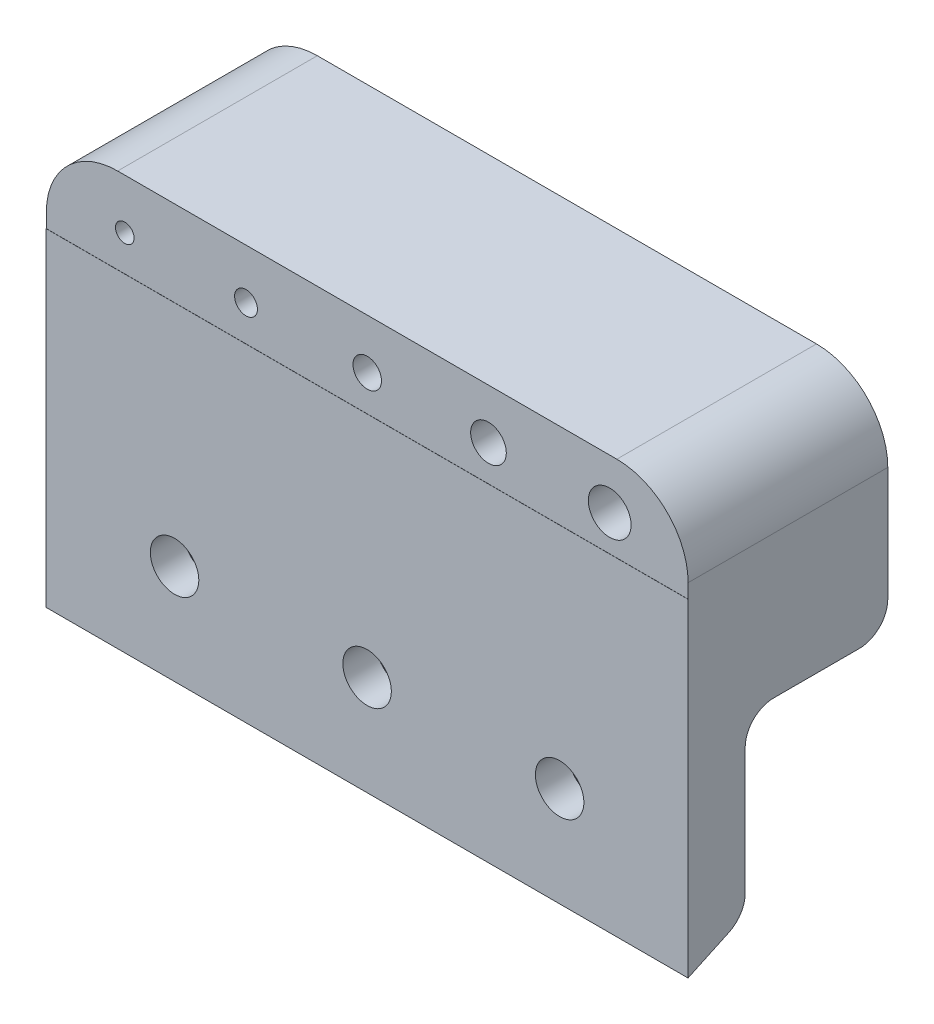
SolidWorks part; units mm, degrees
material "Alliage 2018"
ref_plane "Plan de face" through (0, 0, 0) normal (0, 0, 1) x (1, 0, 0)
ref_plane "Plan de dessus" through (0, 0, 0) normal (0, 1, 0) x (1, 0, 0)
ref_plane "Plan de droite" through (0, 0, 0) normal (1, 0, 0) x (0, 0, -1)
sketch "Esquisse1" plane through (0, 0, 0) normal (0, 0, 1) x (1, 0, 0)
  line L1 (-22.5, -14.5) -> (22.5, -14.5)
  line L2 (-22.5, -14.5) -> (-22.5, 14.5)
  line L3 (-22.5, 14.5) -> (22.5, 14.5)
  line L4 (22.5, -14.5) -> (22.5, 14.5)
  line L5 (-22.5, -14.5) -> (22.5, 14.5) construction
  line L6 (-22.5, 14.5) -> (22.5, -14.5) construction
  point P0 (0, 0)
  dimension "D1" = 29
  dimension "D2" = 45
extrude "Boss.-Extru.1" add sketch "Esquisse1" along normal blind 14 from offset 0
sketch "Esquisse8" plane through (0, 0, 14) normal (0, 0, 1) x (1, 0, 0)
  line L0 (-22.5, 14.5) -> (-22.5, -14.5) construction
  line L1 (22.5, -14.5) -> (-22.5, -14.5)
  line L2 (22.5, -14.5) -> (22.5, 8.5)
  line L3 (22.5, 8.5) -> (-22.5, 8.5)
  line L4 (-22.5, -14.5) -> (-22.5, 8.5)
  dimension "D1" = 23
extrude "Boss.-Extru.2" add sketch "Esquisse8" along normal blind 0.01
sketch "Esquisse3" plane through (0, 0, 14) normal (0, 0, 1) x (1, 0, 0)
  line L0 (-22.5, 8.5) -> (22.5, 8.5) construction
  line L1 (-22.5, 14.5) -> (-22.5, 8.5) construction
  line L2 (22.5, 8.5) -> (22.5, 14.5) construction
  line L3 (-22.5, -14.5) -> (22.5, -14.5) construction
  line L4 (-22.5, 11) -> (22.5, 11) construction
  circle A0 centre (0, 11) radius 1
  circle A1 centre (-8.5, 11) radius 0.8
  circle A2 centre (-17, 11) radius 0.65
  circle A3 centre (8.5, 11) radius 1.25
  circle A4 centre (17, 11) radius 1.5
  dimension "D3" = 8.5
  dimension "D7" = 3
  dimension "D8" = 2.5
  dimension "D9" = 2
  dimension "D10" = 1.6
  dimension "D11" = 1.3
  dimension "D1" = 23
  dimension "D2" = 2.5
  dimension "D4" = 8.5
  dimension "D5" = 8.5
  dimension "D6" = 8.5
extrude "Enlèv. mat.-Extru.2" cut sketch "Esquisse3" against normal through all both and the other way through all
sketch "Esquisse4" plane through (-22.5, 0, 0) normal (-1, 0, 0) x (0, 0, 1)
  line L0 (0, 14.5) -> (0, -14.5) construction
  line L1 (0, -0.5) -> (10, -0.5)
  line L2 (0, -0.5) -> (0, -14.5)
  line L3 (0, -14.5) -> (10, -14.5)
  line L4 (10, -0.5) -> (10, -14.5)
  line L5 (14.01, -14.5) -> (0, -14.5) construction
  dimension "D1" = 10
  dimension "D2" = 14
extrude "Enlèv. mat.-Extru.3" cut sketch "Esquisse4" against normal through all
fillet "Congé1" radius 5 2 edges at (22.5, 14.5, 7) (-22.5, 14.5, 7)
fillet "Congé2" radius 2 1 edges at (0, -0.5, 10)
sketch "Esquisse5" plane through (0, -0.5, 0) normal (0, -1, 0) x (1, 0, 0)
  line L0 (22.5, 5) -> (-22.5, 5) construction
  line L1 (22.5, 8) -> (22.5, 0) construction
  line L2 (-22.5, 8) -> (-22.5, 0) construction
  line L3 (-17, 14) -> (-17, 0) construction
  line L4 (-22.5, 14) -> (22.5, 14) construction
  line L5 (22.5, 0) -> (-22.5, 0) construction
  line L6 (-8.5, 14) -> (-8.5, 0) construction
  line L7 (0, 14) -> (0, 0) construction
  line L8 (8.5, 14) -> (8.5, 0) construction
  line L9 (17, 14) -> (17, 0) construction
  circle A0 centre (17, 5) radius 1.5
  circle A1 centre (8.5, 5) radius 1.5
  circle A2 centre (0, 5) radius 1.5
  circle A3 centre (-8.5, 5) radius 1.5
  circle A4 centre (-17, 5) radius 1.5
  dimension "D1" = 3
  dimension "D2" = 3
  dimension "D3" = 3
  dimension "D4" = 3
  dimension "D5" = 5
extrude "Enlèv. mat.-Extru.4" cut sketch "Esquisse5" against normal blind 13
hole_wizard "Fraisage pour vis à tête fraisée à 6 pans creux M31" positions "Esquisse10" profile "Esquisse9" countersink size "M3" standard "ISO" end condition through all
sketch "Esquisse10" plane through (0, 0, 10) normal (0, 0, -1) x (-1, 0, 0)
  line L0 (22.5, -7.5) -> (-22.5, -7.5) construction
  line L1 (22.5, -14.5) -> (22.5, -2.5) construction
  line L2 (-22.5, -14.5) -> (-22.5, -2.5) construction
  line L5 (-22.5, -14.5) -> (22.5, -14.5) construction
  line L6 (-22.5, -14.5) -> (-22.5, -2.5) construction
  line L7 (22.5, -14.5) -> (22.5, -2.5) construction
  point P0 (-13.5, -7.5)
  point P5 (13.5, -7.5)
  point P28 (0, -7.5)
  dimension "D1" = 7
  dimension "D2" = 9
  dimension "D3" = 9
sketch "Esquisse9" plane through (13.5, -7.5, 10) normal (1, 0, 0) x (0, 1, 0)
  line L0 (0, 0) -> (0, 4.01)
  line L1 (0, 4.01) -> (1.7, 4.01)
  line L2 (1.7, 4.01) -> (1.7, 1.66)
  line L3 (1.7, 1.66) -> (3.36, 0)
  line L5 (3.36, 0) -> (0, 0)
  line L6 (-1.7, 1.66) -> (-3.36, 0) construction
  line L11 (0, -6.35) -> (0, 107.95) construction
  dimension "Diamètre du perçage jusqu'au prochain" = 3.4
  dimension "Profondeur du perçage jusqu'au prochain" = 4.01
  dimension "Diamètre du fraisage entrant" = 6.72
  dimension "Angle du fraisage entrant" = 90
hole_wizard "Trou pour taraudage pour trou taraudé M51" positions "Esquisse12" profile "Esquisse11" hole size "M5" standard "ISO"
sketch "Esquisse12" plane through (0, -0.5, 0) normal (0, -1, 0) x (-1, 0, 0)
  line L0 (22.5, -5) -> (-22.5, -5) construction
  line L1 (22.5, -8) -> (22.5, 0) construction
  line L2 (-22.5, -8) -> (-22.5, 0) construction
  line L5 (-22.5, 0) -> (22.5, 0) construction
  point P0 (17, -5)
  point P3 (8.5, -5)
  point P6 (0, -5)
  point P9 (-8.5, -5)
  point P12 (-17, -5)
  dimension "D1" = 5
sketch "Esquisse11" plane through (-17, -0.5, 5) normal (1, 0, 0) x (0, 0, -1)
  line L0 (0, 0) -> (0, 7.2618)
  line L1 (0, 7.2618) -> (2.1, 6)
  line L2 (2.1, 6) -> (2.1, 0)
  line L5 (2.1, 0) -> (0, 0)
  line L10 (0, 7.2618) -> (-2.1, 6) construction
  line L11 (0, -6.35) -> (0, 107.95) construction
  dimension "Diamètre du perçage" = 4.2
  dimension "Profondeur du perçage" = 6
  dimension "Angle de pointe" = 118
hole_wizard "Dégagement M2.51" positions "Esquisse15" profile "Esquisse14" hole size "M2.5" standard "ISO"
sketch "Esquisse15" plane through (0, 0, 0) normal (0, 0, -1) x (-1, 0, 0)
  line L2 (-22.5, 8.5) -> (22.5, 8.5) construction
  line L7 (-17.5, 14.5) -> (17.5, 14.5) construction
  line L8 (-22.5, -0.5) -> (-22.5, 9.5) construction
  line L9 (22.5, 9.5) -> (22.5, -0.5) construction
  point P0 (-12.5, 8.5)
  point P4 (12.5, 8.5)
  dimension "D1" = 6
  dimension "D2" = 10
  dimension "D3" = 10
sketch "Esquisse14" plane through (12.5, 8.5, 0) normal (1, 0, 0) x (0, 1, 0)
  line L0 (0, 0) -> (0, 5.8712)
  line L1 (0, 5.8712) -> (1.45, 5)
  line L2 (1.45, 5) -> (1.45, 0)
  line L5 (1.45, 0) -> (0, 0)
  line L10 (0, 5.8712) -> (-1.45, 5) construction
  line L11 (0, -6.35) -> (0, 107.95) construction
  dimension "Diamètre du perçage" = 2.9
  dimension "Profondeur du perçage" = 5
  dimension "Angle de pointe" = 118
fillet "Congé4" radius 2 1 edges at (0, -0.5, 0)
chamfer "Chanfrein1" distance 4 distance2 1.865 1 edges at (0, -14.5, 10)
fillet "Congé5" radius 2 1 edges at (0, -12.635, 10)
